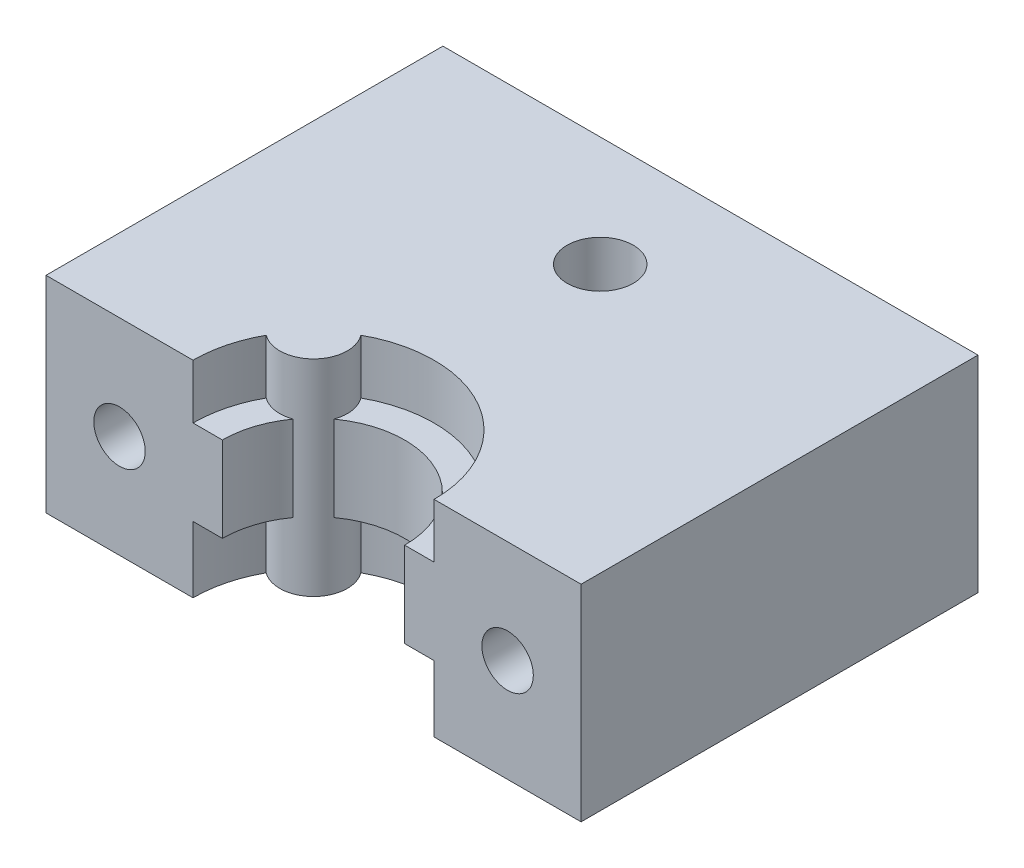
SolidWorks part; units mm, degrees
ref_plane "Front Plane" through (0, 0, 0) normal (0, 0, 1) x (1, 0, 0)
ref_plane "Top Plane" through (0, 0, 0) normal (0, 1, 0) x (1, 0, 0)
ref_plane "Right Plane" through (0, 0, 0) normal (1, 0, 0) x (0, 0, -1)
sketch "Sketch1" plane through (0, 0, 0) normal (0, 0, 1) x (1, 0, 0)
  line L0 (18.2, 14) -> (18.2, 0) construction
  line L1 (0, 0) -> (36.4, 0)
  line L2 (0, 0) -> (0, 14)
  line L3 (0, 14) -> (36.4, 14)
  line L4 (36.4, 0) -> (36.4, 14)
  line L5 (10, 14) -> (10, 0) construction
  line L6 (26.4, 14) -> (26.4, 0) construction
  circle A0 centre (5, 7) radius 1.75 construction
  circle A2 centre (31.4, 7) radius 1.75 construction
  point P9 (0, 7)
  dimension "D1" = 3.5
  dimension "D2" = 16.4
  dimension "D3" = 5
  dimension "D4" = 5
  dimension "D5" = 14
extrude "Boss-Extrude1" add sketch "Sketch1" against normal blind 27
sketch "Sketch2" plane through (0, 14, 0) normal (0, 1, 0) x (1, 0, 0)
  line L0 (36.4, 0) -> (0, 0) construction
  line L1 (10, 0) -> (26.4, 0)
  line L2 (12.4017, 5.7983) -> (18.2, 0) construction
  arc A0 (10, 0) -> (26.4, 0) centre (18.2, 0) cw
  arc A1 (11.0195, 3.9599) -> (14.2401, 7.1805) centre (18.2, 0) cw
  arc A2 (11.0195, 3.9599) -> (14.2401, 7.1805) centre (12.4017, 5.7983) ccw
  point P7 (18.2, 0)
  line M6 (0, 0) -> (36.4, 0)
  dimension "D1" = 2.3
  dimension "D2" = 8.2
  dimension "D3" = 45
extrude "Cut-Extrude1" cut sketch "Sketch2" against normal up to surface (14 mm away) contours A2 L2 L1 A0 | L2 A2 A0 M6
sketch "Sketch4" plane through (0, 14, 0) normal (0, 1, 0) x (1, 0, 0)
  line L0 (12, 0) -> (10, 0)
  line L1 (24.4, 0) -> (26.4, 0)
  arc A0 (12, 0) -> (24.4, 0) centre (18.2, 0) cw
  arc A1 (26.4, 0) -> (14.2401, 7.1805) centre (18.2, 0) ccw construction
  arc A2 (10, 0) -> (26.4, 0) centre (18.2, 0) cw
  dimension "D1" = 2
extrude "Boss-Extrude2" add sketch "Sketch4" against normal blind 5.8 from offset 3.7 offset against normal yes
sketch "Sketch3" plane through (0, 0, 0) normal (0, 0, 1) x (1, 0, 0)
  circle A0 centre (5, 7) radius 1.75
  circle A1 centre (5, 7) radius 1.75 construction
  circle A2 centre (31.4, 7) radius 1.75
  circle A3 centre (31.4, 7) radius 1.75 construction
extrude "Cut-Extrude2" cut sketch "Sketch3" against normal up to surface (27 mm away) up to face at (18.2, 7, -27)
sketch "Sketch5" plane through (0, 0, -27) normal (0, 0, -1) x (-1, 0, 0)
  circle A0 centre (-31.4, 7) radius 3.25
  circle A1 centre (-5, 7) radius 3.25
  dimension "D1" = 6.5
extrude "Cut-Extrude3" cut sketch "Sketch5" against normal blind 5
sketch "Sketch6" plane through (0, 14, 0) normal (0, 1, 0) x (1, 0, 0)
  line L0 (18.2, 0) -> (18.2, 19.5) construction
  circle A0 centre (18.2, 19.5) radius 2.25
  dimension "D2" = 4.5
  dimension "D1" = 19.5
extrude "heat set insert for extruder" cut sketch "Sketch6" against normal blind 7
sketch "Sketch8" plane through (0, 0, -27) normal (0, 0, -1) x (-1, 0, 0)
  line L0 (-36.4, 0) -> (-36.4, 14) construction
  circle A0 centre (-24, 8) radius 2.25
  circle A2 centre (-31.4, 7) radius 1.75 construction
  point P2 (-24.3718, 7)
  point P5 (-36.4, 7)
  point P8 (-24.1417, 8.4414)
  dimension "D1" = 4.5
  dimension "D2" = 1
  dimension "D3" = 7.4
extrude "Cut-Extrude4" cut sketch "Sketch8" against normal blind 4
